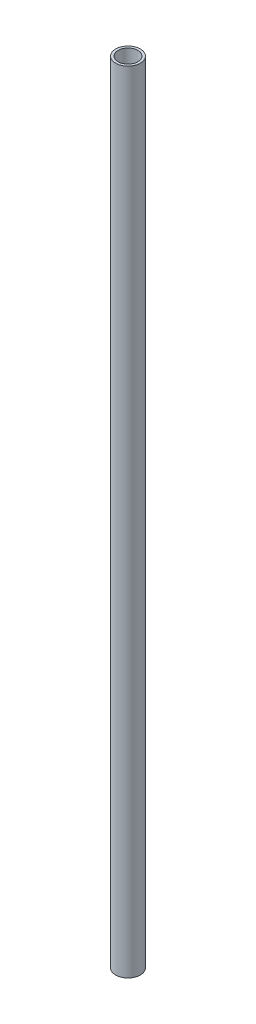
SolidWorks part; units mm, degrees
ref_plane "Front Plane" through (0, 0, 0) normal (0, 0, 1) x (1, 0, 0)
ref_plane "Top Plane" through (0, 0, 0) normal (0, 1, 0) x (1, 0, 0)
ref_plane "Right Plane" through (0, 0, 0) normal (1, 0, 0) x (0, 0, -1)
sketch "Sketch1" plane through (0, 0, 0) normal (0, 1, 0) x (1, 0, 0)
  circle A0 centre (0, 0) radius 4.7625
  circle A1 centre (0, 0) radius 3.81
  dimension "D1" = 9.525
  dimension "D2" = 7.62
extrude "Boss-Extrude1" add sketch "Sketch1" along normal blind 304.8
